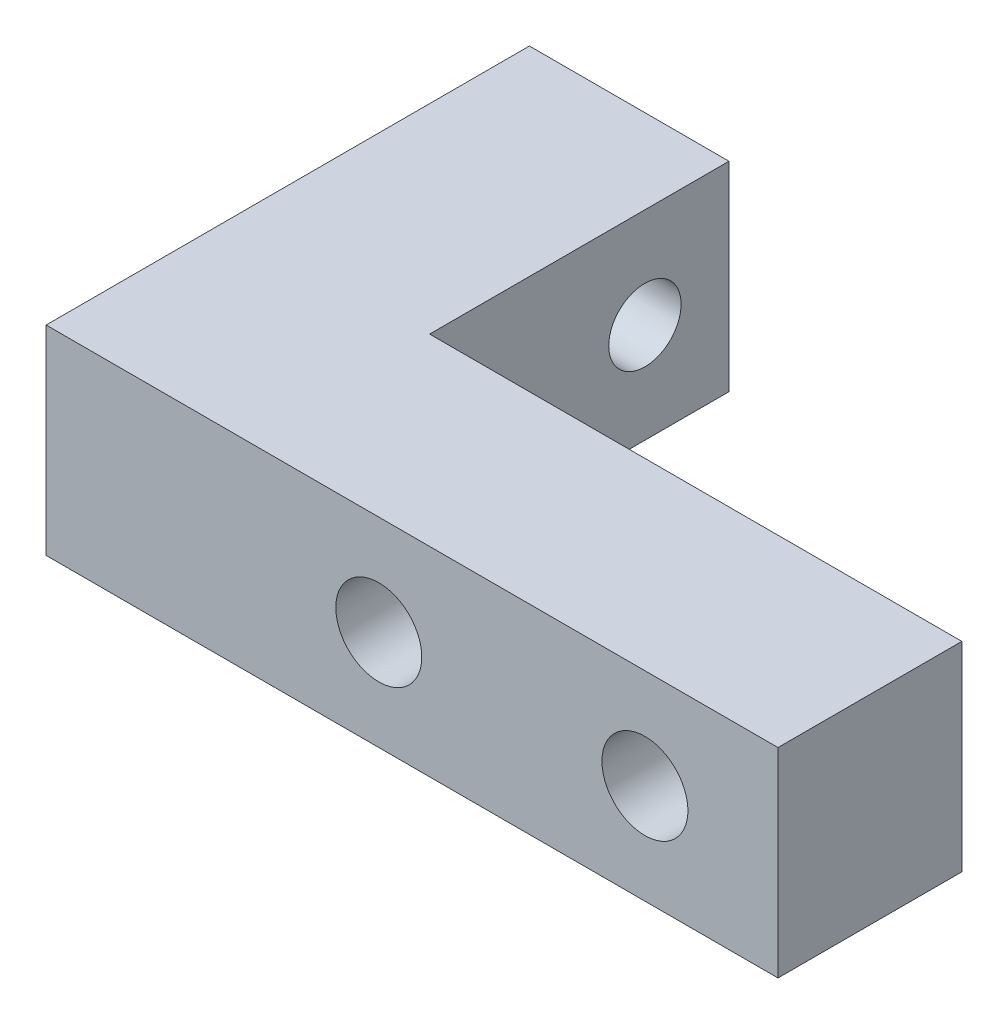
SolidWorks part; units mm, degrees
ref_plane "Front Plane" through (0, 0, 0) normal (0, 0, 1) x (1, 0, 0)
ref_plane "Top Plane" through (0, 0, 0) normal (0, 1, 0) x (1, 0, 0)
ref_plane "Right Plane" through (0, 0, 0) normal (1, 0, 0) x (0, 0, -1)
sketch "Sketch1" plane through (0, 0, 0) normal (0, 1, 0) x (1, 0, 0)
  line L1 (-34.925, -23.8125) -> (34.925, -23.8125)
  line L2 (-34.925, -23.8125) -> (-34.925, 23.8125)
  line L3 (-34.925, 23.8125) -> (34.925, 23.8125)
  line L4 (34.925, -23.8125) -> (34.925, 23.8125)
  line L5 (-34.925, -23.8125) -> (34.925, 23.8125) construction
  line L6 (-34.925, 23.8125) -> (34.925, -23.8125) construction
  point P0 (0, 0)
  dimension "D1" = 69.85
  dimension "D2" = 47.625
extrude "Boss-Extrude1" add sketch "Sketch1" along normal blind 19.05
sketch "Sketch2" plane through (0, 19.05, 0) normal (0, 1, 0) x (1, 0, 0)
  line L0 (-34.925, 23.8125) -> (-34.925, -23.8125) construction
  line L1 (34.925, 23.8125) -> (-15.875, 23.8125)
  line L2 (34.925, 23.8125) -> (34.925, -4.7625)
  line L3 (34.925, -4.7625) -> (-15.875, -4.7625)
  line L4 (-15.875, 23.8125) -> (-15.875, -4.7625)
  line L5 (-34.925, -23.8125) -> (34.925, -23.8125) construction
  dimension "D1" = 19.05
  dimension "D2" = 19.05
extrude "Cut-Extrude1" cut sketch "Sketch2" against normal up to next
hole_wizard "5/16-24 Tapped Hole1" positions "Sketch4" profile "Sketch3" tap size "5/16-24" standard "Ansi Inch"
sketch "Sketch4" plane through (-34.925, 0, 0) normal (-1, 0, 0) x (0, 0, 1)
  line L1 (-23.8125, 9.525) -> (-14.2875, 9.525) construction
  line L2 (-23.8125, 19.05) -> (-23.8125, 0) construction
  line L3 (11.1125, 9.525) -> (-14.2875, 9.525) construction
  line L4 (23.8125, 19.05) -> (23.8125, 0) construction
  point P0 (-14.2875, 9.525)
  point P1 (11.1125, 9.525)
  point P102 (0, 0)
  dimension "D1" = 12.7
  dimension "D2" = 25.4
sketch "Sketch3" plane through (-34.925, 9.525, -14.2875) normal (0, 1, 0) x (0, 0, 1)
  line L0 (0, 0) -> (0, 21.1356)
  line L1 (0, 21.1356) -> (3.4544, 19.06)
  line L2 (3.4544, 19.06) -> (3.4544, 1.1494)
  line L3 (3.4544, 1.1494) -> (4.6037, 0)
  line L5 (4.6037, 0) -> (0, 0)
  line L6 (-3.4544, 1.1494) -> (-4.6037, 0) construction
  line L10 (0, 21.1356) -> (-3.4544, 19.06) construction
  line L11 (0, -6.35) -> (0, 107.95) construction
  dimension "Tap Drill Dia." = 6.9088
  dimension "Tap Drill Depth" = 19.06
  dimension "Near C'Sink Dia." = 9.2075
  dimension "Near C'Sink Angle" = 90
  dimension "Drill Angle" = 118
cosmetic thread "Hole Thread1" parameters "D1"=15.88, "D2"=7.9375
cosmetic thread "Hole Thread2" parameters "D1"=15.88, "D2"=7.9375
hole_wizard "5/16 Clearance Hole1" positions "Sketch6" profile "Sketch5" hole size "5/16" standard "Ansi Inch" end condition through all
sketch "Sketch6" plane through (0, 0, 4.7625) normal (0, 0, -1) x (-1, 0, 0)
  line L0 (3.175, 9.525) -> (-22.225, 9.525) construction
  line L1 (-34.925, 9.525) -> (-22.225, 9.525) construction
  line L2 (-34.925, 0) -> (-34.925, 19.05) construction
  point P0 (3.175, 9.525)
  point P1 (-22.225, 9.525)
  dimension "D1" = 12.7
  dimension "D2" = 25.4
sketch "Sketch5" plane through (-3.175, 9.525, 4.7625) normal (1, 0, 0) x (0, 1, 0)
  line L0 (0, 0) -> (0, 19.05)
  line L1 (0, 19.05) -> (4.1021, 19.05)
  line L2 (4.1021, 19.05) -> (4.1021, 0.635)
  line L3 (4.1021, 0.635) -> (4.7371, 0)
  line L5 (4.7371, 0) -> (0, 0)
  line L6 (-4.1021, 0.635) -> (-4.7371, 0) construction
  line L11 (0, -6.35) -> (0, 107.95) construction
  dimension "Thru Hole Dia." = 8.2042
  dimension "Thru Hole Depth" = 19.05
  dimension "Near C'Sink Dia." = 9.4742
  dimension "Near C'Sink Angle" = 90
chamfer "Chamfer1" distance 1.5 angle 45 6 edges at (9.525, 0, 4.7625) (9.525, 19.05, 4.7625) (34.925, 9.525, 4.7625) (-25.4, 0, -23.8125) (-25.4, 19.05, -23.8125) (-15.875, 9.525, -23.8125)
